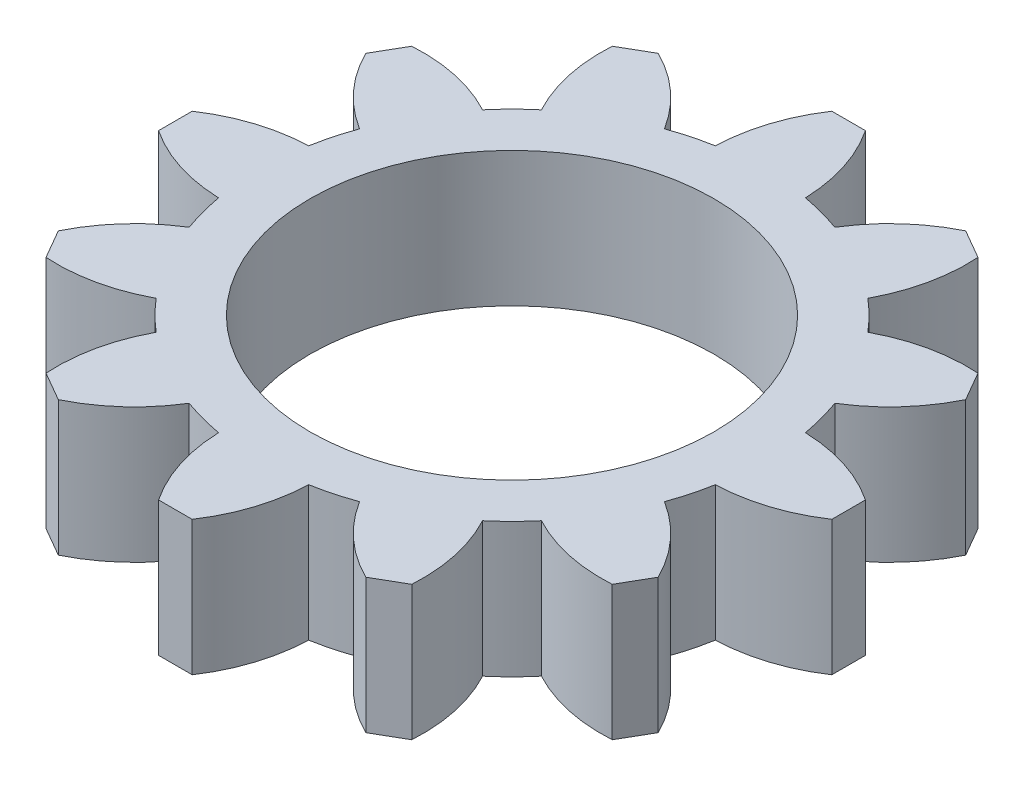
SolidWorks part; units mm, degrees
ref_plane "Front Plane" through (0, 0, 0) normal (0, 0, 1) x (1, 0, 0)
ref_plane "Top Plane" through (0, 0, 0) normal (0, 1, 0) x (1, 0, 0)
ref_plane "Right Plane" through (0, 0, 0) normal (1, 0, 0) x (0, 0, -1)
sketch "Sketch1" plane through (0, 0, 0) normal (0, 1, 0) x (1, 0, 0)
  line L0 (0, 0) -> (0, 18.9151) construction
  line L1 (-1, 20) -> (1, 20)
  line L2 (9.134, 17.8205) -> (10.866, 16.8205)
  line L3 (16.8205, 10.866) -> (17.8205, 9.134)
  line L4 (20, 1) -> (20, -1)
  line L5 (17.8205, -9.134) -> (16.8205, -10.866)
  line L6 (10.866, -16.8205) -> (9.134, -17.8205)
  line L7 (1, -20) -> (-1, -20)
  line L8 (-9.134, -17.8205) -> (-10.866, -16.8205)
  line L9 (-16.8205, -10.866) -> (-17.8205, -9.134)
  line L10 (-20, -1) -> (-20, 1)
  line L11 (-17.8205, 9.134) -> (-16.8205, 10.866)
  line L12 (-10.866, 16.8205) -> (-9.134, 17.8205)
  circle A0 centre (0, 0) radius 12
  arc A1 (-2.675, 14.7596) -> (-5.0632, 14.1196) centre (0, 0) ccw
  arc A2 (-1, 20) -> (-2.675, 14.7596) centre (7.3203, 14.4527) ccw
  arc A3 (1, 20) -> (2.675, 14.7596) centre (-7.3203, 14.4527) cw
  arc A4 (10.866, 16.8205) -> (9.6964, 11.4446) centre (0.8868, 16.1765) cw
  arc A5 (9.134, 17.8205) -> (5.0632, 14.1196) centre (13.5659, 8.8562) ccw
  arc A6 (17.8205, 9.134) -> (14.1196, 5.0632) centre (8.8562, 13.5659) cw
  arc A7 (16.8205, 10.866) -> (11.4446, 9.6964) centre (16.1765, 0.8868) ccw
  arc A8 (20, -1) -> (14.7596, -2.675) centre (14.4527, 7.3203) cw
  arc A9 (20, 1) -> (14.7596, 2.675) centre (14.4527, -7.3203) ccw
  arc A10 (16.8205, -10.866) -> (11.4446, -9.6964) centre (16.1765, -0.8868) cw
  arc A11 (17.8205, -9.134) -> (14.1196, -5.0632) centre (8.8562, -13.5659) ccw
  arc A12 (9.134, -17.8205) -> (5.0632, -14.1196) centre (13.5659, -8.8562) cw
  arc A13 (10.866, -16.8205) -> (9.6964, -11.4446) centre (0.8868, -16.1765) ccw
  arc A14 (-1, -20) -> (-2.675, -14.7596) centre (7.3203, -14.4527) cw
  arc A15 (1, -20) -> (2.675, -14.7596) centre (-7.3203, -14.4527) ccw
  arc A16 (-10.866, -16.8205) -> (-9.6964, -11.4446) centre (-0.8868, -16.1765) cw
  arc A17 (-9.134, -17.8205) -> (-5.0632, -14.1196) centre (-13.5659, -8.8562) ccw
  arc A18 (-17.8205, -9.134) -> (-14.1196, -5.0632) centre (-8.8562, -13.5659) cw
  arc A19 (-16.8205, -10.866) -> (-11.4446, -9.6964) centre (-16.1765, -0.8868) ccw
  arc A20 (-20, 1) -> (-14.7596, 2.675) centre (-14.4527, -7.3203) cw
  arc A21 (-20, -1) -> (-14.7596, -2.675) centre (-14.4527, 7.3203) ccw
  arc A22 (-16.8205, 10.866) -> (-11.4446, 9.6964) centre (-16.1765, 0.8868) cw
  arc A23 (-17.8205, 9.134) -> (-14.1196, 5.0632) centre (-8.8562, 13.5659) ccw
  arc A24 (-9.134, 17.8205) -> (-5.0632, 14.1196) centre (-13.5659, 8.8562) cw
  arc A25 (-10.866, 16.8205) -> (-9.6964, 11.4446) centre (-0.8868, 16.1765) ccw
  arc A26 (-9.6964, 11.4446) -> (-11.4446, 9.6964) centre (0, 0) ccw
  arc A27 (-14.1196, 5.0632) -> (-14.7596, 2.675) centre (0, 0) ccw
  arc A28 (-14.7596, -2.675) -> (-14.1196, -5.0632) centre (0, 0) ccw
  arc A29 (-11.4446, -9.6964) -> (-9.6964, -11.4446) centre (0, 0) ccw
  arc A30 (-5.0632, -14.1196) -> (-2.675, -14.7596) centre (0, 0) ccw
  arc A31 (2.675, -14.7596) -> (5.0632, -14.1196) centre (0, 0) ccw
  arc A32 (9.6964, -11.4446) -> (11.4446, -9.6964) centre (0, 0) ccw
  arc A33 (14.1196, -5.0632) -> (14.7596, -2.675) centre (0, 0) ccw
  arc A34 (14.7596, 2.675) -> (14.1196, 5.0632) centre (0, 0) ccw
  arc A35 (11.4446, 9.6964) -> (9.6964, 11.4446) centre (0, 0) ccw
  arc A36 (5.0632, 14.1196) -> (2.675, 14.7596) centre (0, 0) ccw
  point P80 (0, 0)
  dimension "D1" = 30
  dimension "D2" = 24
  dimension "D5" = 10
  dimension "D3" = 2
  dimension "D4" = 20
  dimension "D6" = 5.35
  dimension "D7" = 12
extrude "Boss-Extrude1" add sketch "Sketch1" along normal mid plane 8
